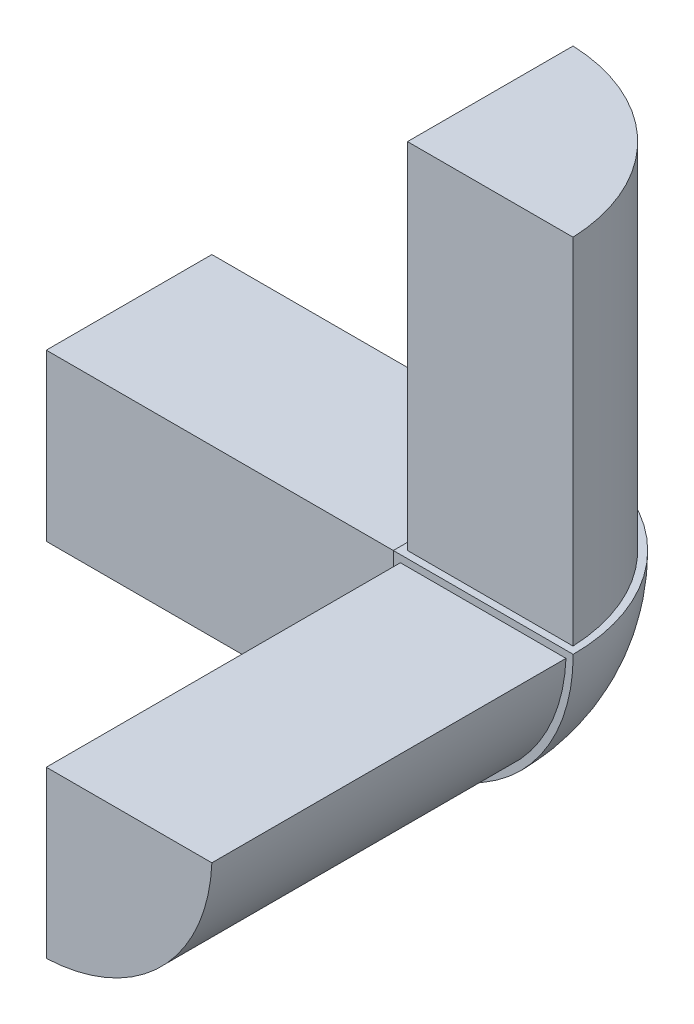
SolidWorks part; units mm, degrees
ref_plane "Alzado" through (0, 0, 0) normal (0, 0, 1) x (1, 0, 0)
ref_plane "Planta" through (0, 0, 0) normal (0, 1, 0) x (1, 0, 0)
ref_plane "Vista lateral" through (0, 0, 0) normal (1, 0, 0) x (0, 0, -1)
sketch "Croquis1" plane through (0, 0, 0) normal (0, 0, 1) x (1, 0, 0)
  line L0 (0, 32.8991) -> (0, -36.1985) construction
  line L1 (0, 25.4) -> (0, -25.4)
  arc A1 (0, 25.4) -> (0, -25.4) centre (0, 0) cw
  dimension "D2" = 25.4
  dimension "D1" = 50.8
revolve "Revolución1" add sketch "Croquis1" angle 360 about L0
sketch "Croquis2" plane through (0, 0, 0) normal (0, 1, 0) x (1, 0, 0)
  line L0 (-36.0622, 0) -> (37.5596, 0) construction
  line L1 (0, 40.8418) -> (0, -30.0373) construction
  line L2 (0, 25.4) -> (0, 0)
  line L3 (0, 0) -> (25.4, 0)
  circle A0 centre (0, 0) radius 25.4 construction
  arc A1 (0, 25.4) -> (25.4, 0) centre (0, 0) cw
  dimension "D1" = 25.4
extrude "Saliente-Extruir1" add sketch "Croquis2" along normal blind 50
sketch "Croquis3" plane through (0, 0, 0) normal (0, 0, 1) x (1, 0, 0)
  line L0 (0, 0) -> (25.4, 0)
  line L1 (0, 0) -> (0, -25.4)
  arc A0 (0, 25.4) -> (25.4, 0) centre (0, 0) ccw construction
  arc A1 (0, -25.4) -> (25.4, 0) centre (0, 0) ccw
  dimension "D1" = 25.4
extrude "Saliente-Extruir2" add sketch "Croquis3" along normal blind 50
sketch "Croquis4" plane through (0, 0, 0) normal (1, 0, 0) x (0, 0, -1)
  line L0 (25.4, 0) -> (0, 0)
  line L1 (25.4, 50) -> (25.4, 0) construction
  line L2 (0, 0) -> (0, -25.4)
  arc A0 (0, -25.4) -> (25.4, 0) centre (0, 0) ccw construction
  arc A1 (0, -25.4) -> (25.4, 0) centre (0, 0) ccw
  dimension "D1" = 25.4
extrude "Saliente-Extruir3" add sketch "Croquis4" against normal blind 50
sketch "Croquis5" plane through (0, 0, 0) normal (0, 0, 1) x (1, 0, 0)
  line L0 (0, 25.4) -> (0, 0)
  line L1 (0, 0) -> (-25.4, 0)
  arc A0 (-25.4, 0) -> (0, 25.4) centre (0, 0) cw
  dimension "D1" = 25.4
extrude "Cortar-Extruir1" cut sketch "Croquis5" against normal mid plane 60
sketch "Croquis8" plane through (0, 0, 0) normal (1, 0, 0) x (0, 0, -1)
  line L1 (0, 0) -> (-25.4, 0)
  line L2 (0, 0) -> (0, 25.4)
  line L3 (0, 25.4) -> (-25.4, 25.4)
  line L4 (-25.4, 0) -> (-25.4, 25.4)
  dimension "D1" = 25.4
extrude "Cortar-Extruir5" cut sketch "Croquis8" along normal blind 50
sketch "Croquis9" plane through (0, 0, 0) normal (0, 1, 0) x (1, 0, 0)
  line L1 (0, 0) -> (-25.4, 0)
  line L2 (0, 0) -> (0, -25.4)
  line L3 (0, -25.4) -> (-25.4, -25.4)
  line L4 (-25.4, 0) -> (-25.4, -25.4)
  dimension "D1" = 25.4
  dimension "D2" = 25.4
extrude "Cortar-Extruir6" cut sketch "Croquis9" against normal blind 50
sketch "Croquis11" plane through (-50, 0, 0) normal (-1, 0, 0) x (0, 0, 1)
  line L0 (-1, -24.3795) -> (-1, -1)
  line L1 (-1, -1) -> (-24.3795, -1)
  line L2 (0, -25.4) -> (0, 0)
  line L3 (0, 0) -> (-25.4, 0)
  line L4 (0, -25.4) -> (0, 0)
  line L5 (0, 0) -> (-25.4, 0)
  arc A0 (-24.3795, -1) -> (-1, -24.3795) centre (0, 0) ccw
  arc A1 (-25.4, 0) -> (0, -25.4) centre (0, 0) ccw
  arc A2 (-25.4, 0) -> (0, -25.4) centre (0, 0) ccw
  dimension "D1" = 0
  dimension "D2" = 1
extrude "Cortar-Extruir7" cut sketch "Croquis11" against normal blind 50
sketch "Croquis12" plane through (0, 50, 0) normal (0, 1, 0) x (1, 0, 0)
  line L0 (1, 24.3795) -> (1, 1)
  line L1 (1, 1) -> (24.3795, 1)
  line L2 (0, 25.4) -> (0, 0)
  line L3 (0, 0) -> (25.4, 0)
  line L4 (0, 25.4) -> (0, 0)
  line L5 (0, 0) -> (25.4, 0)
  arc A0 (24.3795, 1) -> (1, 24.3795) centre (0, 0) ccw
  arc A1 (25.4, 0) -> (0, 25.4) centre (0, 0) ccw
  arc A2 (25.4, 0) -> (0, 25.4) centre (0, 0) ccw
  dimension "D1" = 0
  dimension "D2" = 1
extrude "Cortar-Extruir8" cut sketch "Croquis12" against normal blind 50
sketch "Croquis13" plane through (0, 0, 50) normal (0, 0, 1) x (1, 0, 0)
  line L4 (1, -1) -> (1, -24.3795)
  line L5 (24.3795, -1) -> (1, -1)
  line L6 (1, -1) -> (1, -24.3795)
  line L7 (24.3795, -1) -> (1, -1)
  line L8 (0, 0) -> (0, -25.4)
  line L9 (25.4, 0) -> (0, 0)
  line L10 (0, 0) -> (0, -25.4)
  line L11 (25.4, 0) -> (0, 0)
  arc A2 (1, -24.3795) -> (24.3795, -1) centre (0, 0) ccw
  arc A3 (1, -24.3795) -> (24.3795, -1) centre (0, 0) ccw
  arc A4 (0, -25.4) -> (25.4, 0) centre (0, 0) ccw
  arc A5 (0, -25.4) -> (25.4, 0) centre (0, 0) ccw
  dimension "D1" = 1
  dimension "D2" = 0
extrude "Cortar-Extruir9" cut sketch "Croquis13" against normal blind 50
